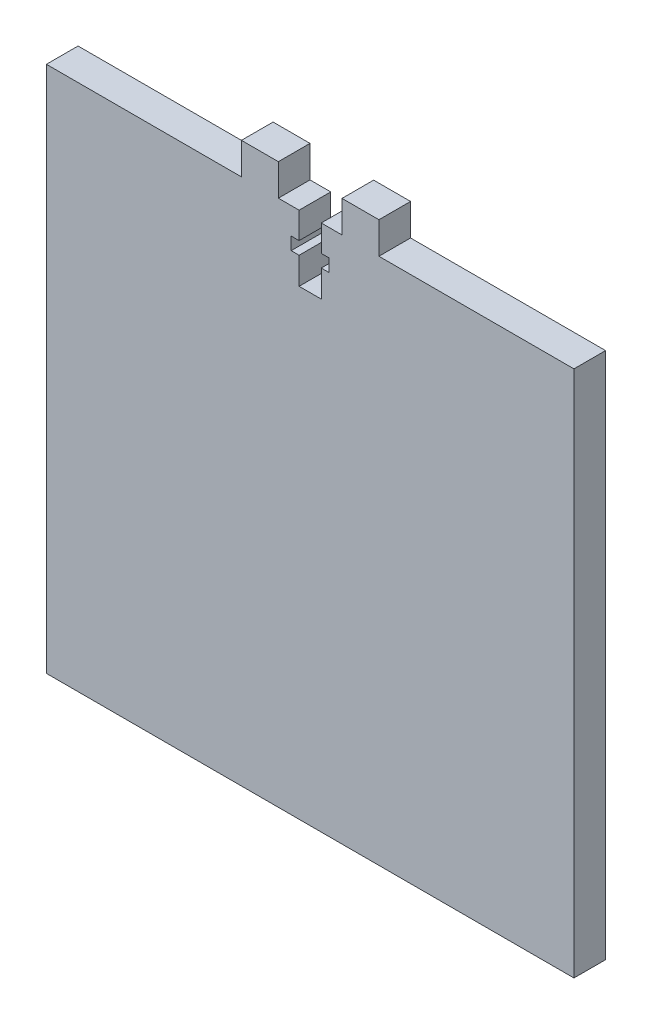
SolidWorks part; units mm, degrees
material "Клен"
ref_plane "Спереди" through (0, 0, 0) normal (0, 0, 1) x (1, 0, 0)
ref_plane "Сверху" through (0, 0, 0) normal (0, 1, 0) x (1, 0, 0)
ref_plane "Справа" through (0, 0, 0) normal (1, 0, 0) x (0, 0, -1)
sketch "Эскиз1" plane through (0, 0, 0) normal (0, 0, 1) x (1, 0, 0)
  line L1 (-50, -50) -> (50, -50)
  line L2 (-50, -50) -> (-50, 50)
  line L3 (-50, 50) -> (50, 50)
  line L4 (50, -50) -> (50, 50)
  line L5 (-50, -50) -> (50, 50) construction
  line L6 (-50, 50) -> (50, -50) construction
  point P0 (0, 0)
  dimension "D1" = 100
extrude "Бобышка-Вытянуть1" add sketch "Эскиз1" along normal blind 6
ref_plane "Плоскость1" through (0, 0, 3) normal (0, 0, 1) x (1, 0, 0)
sketch "Эскиз2" plane through (0, 0, 6) normal (0, 0, 1) x (1, 0, 0)
  line L0 (50, 50) -> (-50, 50) construction
  line L1 (-13.0318, 50) -> (-6.0318, 50)
  line L2 (-13.0318, 50) -> (-13.0318, 56)
  line L3 (-13.0318, 56) -> (-6.0318, 56)
  line L4 (-6.0318, 50) -> (-6.0318, 56)
  line L5 (13, 56) -> (-13, 56) construction
  line L6 (0, 53.4074) -> (0, -162.0434) construction
  line L7 (13.0318, 50) -> (6.0318, 50)
  line L8 (6.0318, 50) -> (6.0318, 56)
  line L9 (13.0318, 56) -> (6.0318, 56)
  line L10 (13.0318, 50) -> (13.0318, 56)
  dimension "D1" = 7
extrude "Бобышка-Вытянуть2" add sketch "Эскиз2" against normal blind 6
sketch "Эскиз3" plane through (0, 0, 6) normal (0, 0, 1) x (1, 0, 0)
  line L1 (6.0318, 50) -> (-6.0318, 50) construction
  line L3 (-2.1, 45) -> (-3.6, 45)
  line L4 (-3.6, 45) -> (-3.6, 42.6)
  line L5 (-3.6, 42.6) -> (-2.1, 42.6)
  line L8 (0, 53.4074) -> (0, -162.0434) construction
  line L11 (3.6, 42.6) -> (2.1, 42.6)
  line L12 (3.6, 45) -> (3.6, 42.6)
  line L13 (2.1, 45) -> (3.6, 45)
  line L16 (-2.1, 45) -> (-2.1, 50)
  line L17 (-2.1, 50) -> (2.1, 50)
  line L18 (2.1, 50) -> (2.1, 45)
  line L19 (2.1, 42.6) -> (2.1, 37.5)
  line L20 (2.1, 37.5) -> (-2.1, 37.5)
  line L21 (-2.1, 37.5) -> (-2.1, 42.6)
  line L23 (-13.0318, 50) -> (-50, 50) construction
  point P15 (0, 43.65)
  point P20 (0, 50)
  dimension "D1" = 5
  dimension "D2" = 7.2
  dimension "D3" = 2.4
  dimension "D4" = 4.2
  dimension "D5" = 12.5
extrude "Вырез-Вытянуть1" cut sketch "Эскиз3" against normal through all
